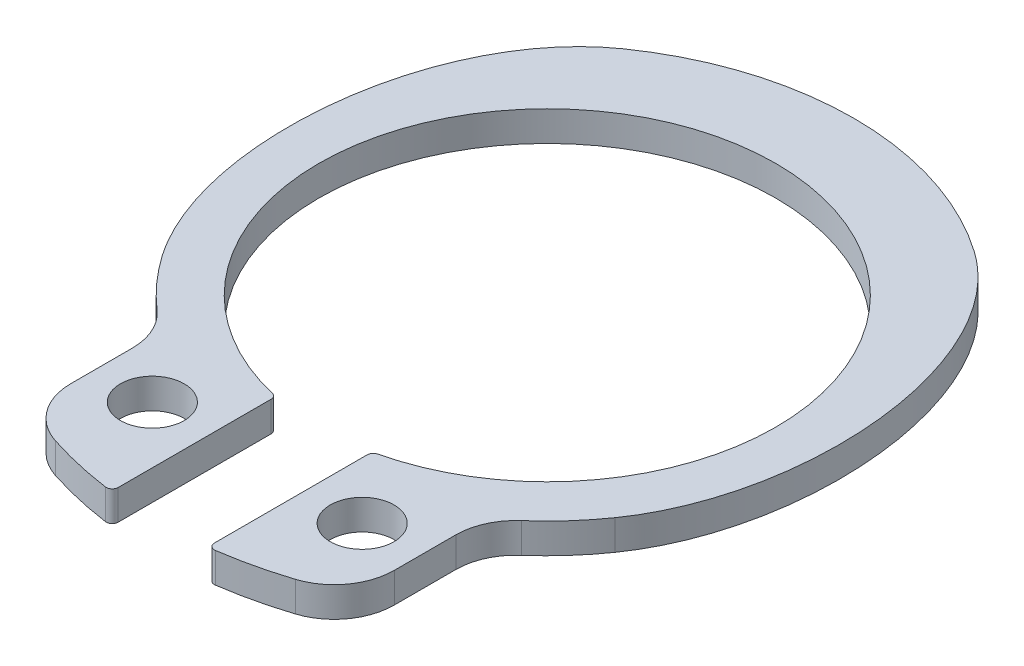
SolidWorks part; units mm, degrees
material "AISI 304"
ref_plane "Front Plane" through (0, 0, 0) normal (0, 0, 1) x (1, 0, 0)
ref_plane "Top Plane" through (0, 0, 0) normal (0, 1, 0) x (1, 0, 0)
ref_plane "Right Plane" through (0, 0, 0) normal (1, 0, 0) x (0, 0, -1)
ref_plane "Piano1" through (0, 0.125, 0) normal (0, 1, 0) x (1, 0, 0)
sketch "Schizzo1" plane through (0, 0.125, 0) normal (0, 1, 0) x (1, 0, 0)
  line L0 (-0.4, -3.1682) -> (-0.4, -1.8974)
  line L1 (0.4, -1.8974) -> (0.4, -3.1682)
  line L2 (1.345, -2.617) -> (1.345, -2.1062)
  line L3 (-1.345, -2.1062) -> (-1.345, -2.617)
  circle A0 centre (0.8725, -2.4122) radius 0.2651
  circle A1 centre (-0.8725, -2.4122) radius 0.2651
  arc A2 (-0.4, -1.8974) -> (-0.4385, -1.8487) centre (-0.45, -1.8974) ccw
  arc A3 (-0.4385, -1.8487) -> (0.4385, -1.8487) centre (0, 0) cw
  arc A4 (0.4385, -1.8487) -> (0.4, -1.8974) centre (0.45, -1.8974) ccw
  arc A5 (0.4, -3.1682) -> (0.457, -3.2177) centre (0.45, -3.1682) ccw
  arc A6 (0.457, -3.2177) -> (0.9986, -3.0928) centre (0, 0) ccw
  arc A7 (0.9986, -3.0928) -> (1.345, -2.617) centre (0.845, -2.617) ccw
  arc A8 (1.345, -2.1062) -> (1.5155, -1.7301) centre (1.845, -2.1062) cw
  arc A9 (1.5155, -1.7301) -> (1.884, -1.3192) centre (0, 0) ccw
  arc A10 (1.4626, 2.0888) -> (-1.4626, 2.0888) centre (0, 0) ccw
  arc A11 (-1.884, -1.3192) -> (-1.5155, -1.7301) centre (0, 0) ccw
  arc A12 (-1.5155, -1.7301) -> (-1.345, -2.1062) centre (-1.845, -2.1062) cw
  arc A13 (-1.345, -2.617) -> (-0.9986, -3.0928) centre (-0.845, -2.617) ccw
  arc A14 (-0.9986, -3.0928) -> (-0.457, -3.2177) centre (0, 0) ccw
  arc A15 (-0.457, -3.2177) -> (-0.4, -3.1682) centre (-0.45, -3.1682) ccw
  spline S0 degree 3 poles (1.884, -1.3192) (2.019, -1.1265) (2.1151, -0.9044) (2.1795, -0.678) (2.2702, -0.359) (2.3025, -0.0199) (2.2854, 0.3113) (2.2678, 0.6509) (2.1976, 0.9944) (2.0639, 1.307) (1.9846, 1.4925) (1.8808, 1.6707) (1.7503, 1.8245) (1.666, 1.9238) (1.5693, 2.0141) (1.4626, 2.0888) knots 0 0 0 0 0.000706 0.000706 0.000706 0.001704 0.001704 0.001704 0.002728 0.002728 0.002728 0.003331 0.003331 0.003331 0.003718 0.003718 0.003718 0.003718
  spline S1 degree 3 poles (-1.4626, 2.0888) (-1.6155, 1.9818) (-1.7479, 1.842) (-1.8545, 1.6888) (-1.9955, 1.4862) (-2.0978, 1.2546) (-2.1673, 1.0178) (-2.2644, 0.6872) (-2.3024, 0.3351) (-2.2861, -0.0091) (-2.2697, -0.3584) (-2.1968, -0.7141) (-2.0491, -1.0311) (-2.0023, -1.1314) (-1.9475, -1.2286) (-1.884, -1.3192) knots 0 0 0 0 0.00056 0.00056 0.00056 0.001301 0.001301 0.001301 0.002339 0.002339 0.002339 0.003396 0.003396 0.003396 0.003724 0.003724 0.003724 0.003724
extrude "Estrusione-Estrusione1" add sketch "Schizzo1" against normal blind 0.25
